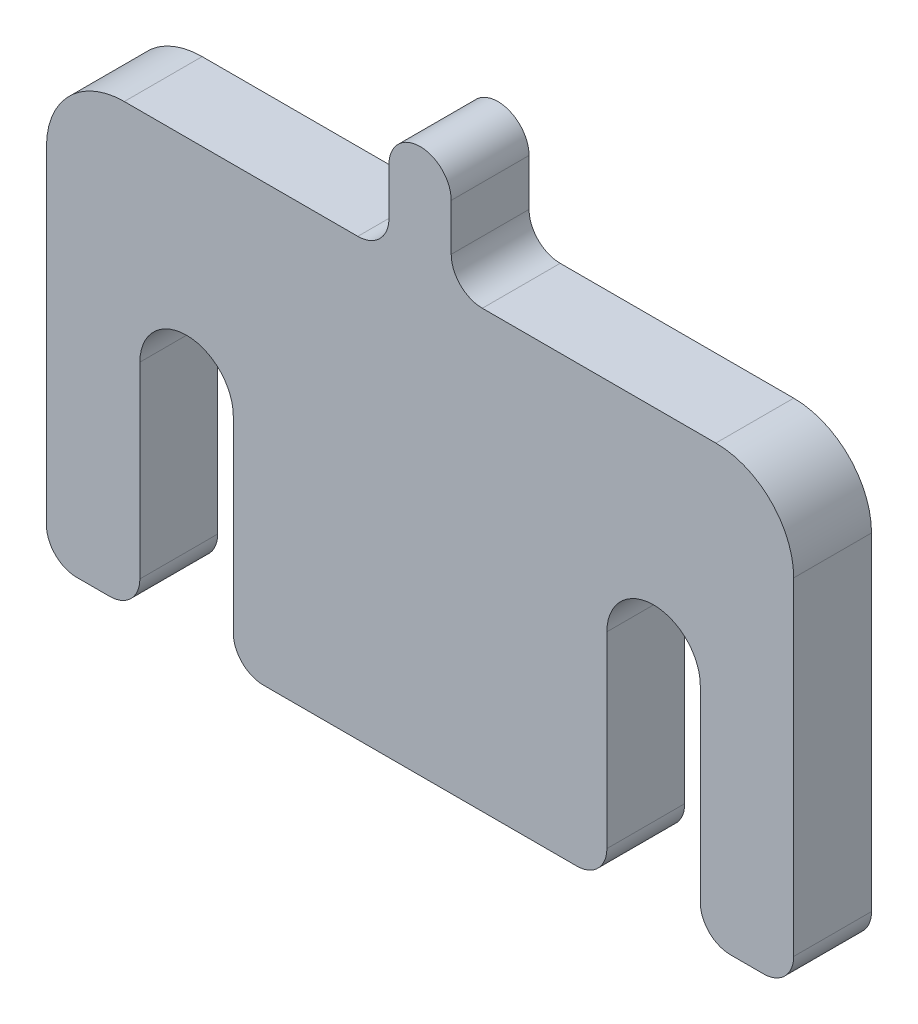
SolidWorks part; units mm, degrees
material "7075-O (SS)"
ref_plane "Płaszczyzna XY" through (0, 0, 0) normal (0, 0, 1) x (1, 0, 0)
ref_plane "Płaszczyzna XZ" through (0, 0, 0) normal (0, 1, 0) x (1, 0, 0)
ref_plane "Płaszczyzna YZ" through (0, 0, 0) normal (1, 0, 0) x (0, 0, -1)
sketch "Szkic1" plane through (0, 0, 0) normal (0, 0, 1) x (1, 0, 0)
  line L0 (15, 0) -> (-15, 0) construction
  line L1 (18, 0) -> (18, -12.0597)
  line L2 (22.0597, -14) -> (19.9403, -14)
  line L3 (24, -12.0597) -> (24, 9)
  line L4 (19, 14) -> (4, 14)
  line L5 (-24, -12.0597) -> (-24, 9)
  line L6 (24, -14) -> (-24, 14) construction
  line L7 (24, 14) -> (-24, -14) construction
  line L8 (12, 0) -> (12, -12.0597)
  line L9 (-12, 0) -> (-12, -12.0597)
  line L10 (-18, 0) -> (-18, -12.0597)
  line L11 (2, 19) -> (2, 16)
  line L12 (-2, 19) -> (-2, 16)
  line L13 (0, 19) -> (0, 0) construction
  line L14 (-4, 14) -> (-19, 14)
  line L15 (10.0597, -14) -> (-10.0597, -14)
  line L16 (-19.9403, -14) -> (-22.0597, -14)
  arc A0 (-12, 0) -> (-18, 0) centre (-15, 0) ccw
  arc A1 (18, 0) -> (12, 0) centre (15, 0) ccw
  arc A2 (2, 19) -> (-2, 19) centre (0, 19) ccw
  arc A3 (-24, 9) -> (-19, 14) centre (-19, 9) cw
  arc A4 (24, 9) -> (19, 14) centre (19, 9) ccw
  arc A5 (-24, -12.0597) -> (-22.0597, -14) centre (-22.0597, -12.0597) ccw
  arc A6 (-19.9403, -14) -> (-18, -12.0597) centre (-19.9403, -12.0597) ccw
  arc A7 (-12, -12.0597) -> (-10.0597, -14) centre (-10.0597, -12.0597) ccw
  arc A8 (10.0597, -14) -> (12, -12.0597) centre (10.0597, -12.0597) ccw
  arc A9 (18, -12.0597) -> (19.9403, -14) centre (19.9403, -12.0597) ccw
  arc A10 (22.0597, -14) -> (24, -12.0597) centre (22.0597, -12.0597) ccw
  arc A11 (-4, 14) -> (-2, 16) centre (-4, 16) ccw
  arc A12 (4, 14) -> (2, 16) centre (4, 16) cw
  point P1 (0, 0)
  point P6 (0, 0)
  point P34 (-18, -14)
  point P37 (-12, -14)
  point P40 (12, -14)
  point P49 (-2, 14)
  dimension "D1" = 30
  dimension "D2" = 6
  dimension "D3" = 28
  dimension "D5" = 4
  dimension "D6" = 5
  dimension "D7" = 5
  dimension "D8" = 1.9403
  dimension "D9" = 2
  dimension "D4" = 48
extrude "Dodanie-wyciągnięcie1" add sketch "Szkic1" along normal blind 5 contours A1 L1 L2 L3 L4 L5 L10 A0 L9 L8 | A2 L12 L4 L11 | A2
